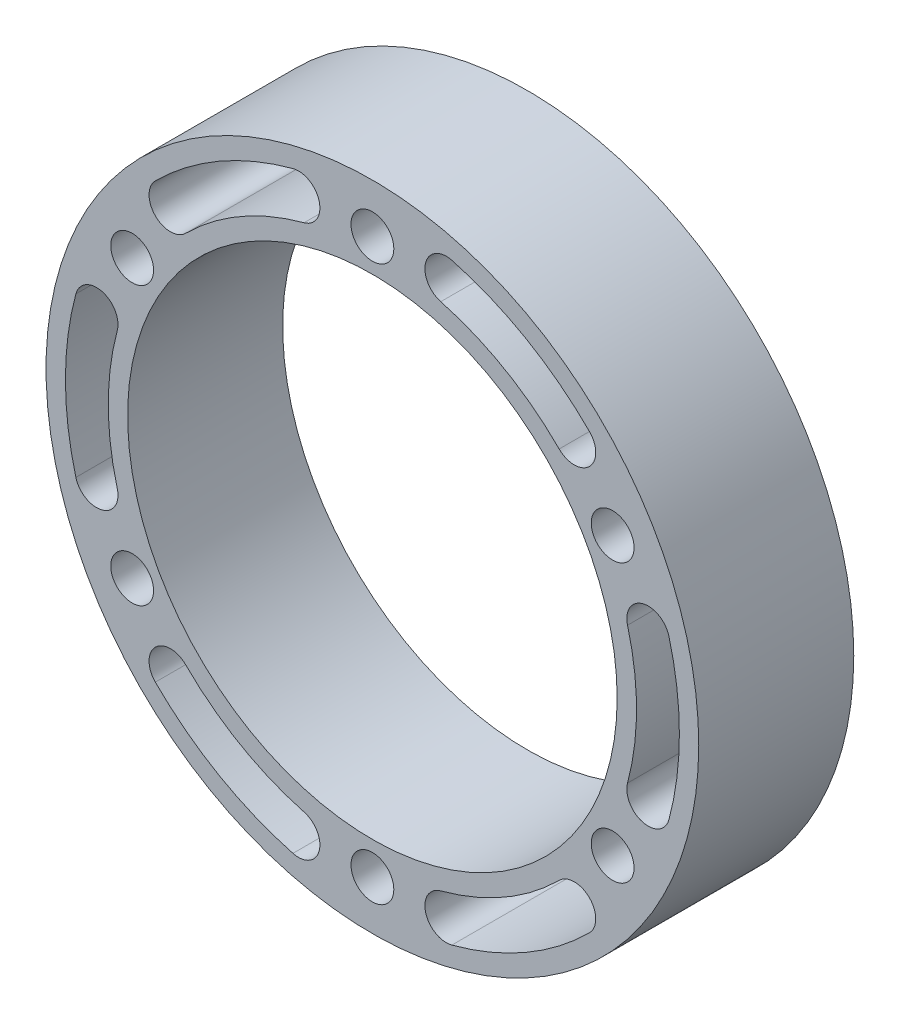
SolidWorks part; units mm, degrees
material "6061-T6 (SS)"
ref_plane "Front Plane" through (0, 0, 0) normal (0, 0, 1) x (1, 0, 0)
ref_plane "Top Plane" through (0, 0, 0) normal (0, 1, 0) x (1, 0, 0)
ref_plane "Right Plane" through (0, 0, 0) normal (1, 0, 0) x (0, 0, -1)
sketch "Sketch1" plane through (0, 0, 0) normal (0, 0, 1) x (1, 0, 0)
  line L0 (0, 0) -> (0, 34) construction
  line L1 (0, 0) -> (-24.7487, 24.7487) construction
  line L2 (0, 0) -> (-9.0587, 33.8074) construction
  line L3 (-29.4449, 17) -> (0, 0) construction
  line L4 (0, 0) -> (-33.8074, -9.0587) construction
  line L5 (-29.4449, -17) -> (0, 0) construction
  circle A0 centre (0, 0) radius 30
  circle A1 centre (0, 0) radius 40
  circle A2 centre (0, 0) radius 34 construction
  circle A3 centre (0, 34) radius 2.625
  circle A4 centre (29.4449, 17) radius 2.625
  circle A5 centre (29.4449, -17) radius 2.625
  circle A6 centre (0, -34) radius 2.625
  circle A7 centre (-29.4449, -17) radius 2.625
  circle A8 centre (-29.4449, 17) radius 2.625
  arc A15 (-9.0587, 33.8074) -> (-24.7487, 24.7487) centre (0, 0) ccw construction
  arc A16 (-9.7381, 36.343) -> (-26.6049, 26.6049) centre (0, 0) ccw
  arc A17 (-8.3793, 31.2718) -> (-22.8926, 22.8926) centre (0, 0) ccw
  arc A18 (-8.3793, 31.2718) -> (-9.7381, 36.343) centre (-9.0587, 33.8074) ccw
  arc A19 (-26.6049, 26.6049) -> (-22.8926, 22.8926) centre (-24.7487, 24.7487) ccw
  arc A20 (24.7487, 24.7487) -> (9.0587, 33.8074) centre (0, 0) ccw construction
  arc A21 (26.6049, 26.6049) -> (9.7381, 36.343) centre (0, 0) ccw
  arc A22 (22.8926, 22.8926) -> (8.3793, 31.2718) centre (0, 0) ccw
  arc A23 (22.8926, 22.8926) -> (26.6049, 26.6049) centre (24.7487, 24.7487) ccw
  arc A24 (9.7381, 36.343) -> (8.3793, 31.2718) centre (9.0587, 33.8074) ccw
  arc A25 (33.8074, -9.0587) -> (33.8074, 9.0587) centre (0, 0) ccw construction
  arc A26 (36.343, -9.7381) -> (36.343, 9.7381) centre (0, 0) ccw
  arc A27 (31.2718, -8.3793) -> (31.2718, 8.3793) centre (0, 0) ccw
  arc A28 (31.2718, -8.3793) -> (36.343, -9.7381) centre (33.8074, -9.0587) ccw
  arc A29 (36.343, 9.7381) -> (31.2718, 8.3793) centre (33.8074, 9.0587) ccw
  arc A30 (9.0587, -33.8074) -> (24.7487, -24.7487) centre (0, 0) ccw construction
  arc A31 (9.7381, -36.343) -> (26.6049, -26.6049) centre (0, 0) ccw
  arc A32 (8.3793, -31.2718) -> (22.8926, -22.8926) centre (0, 0) ccw
  arc A33 (8.3793, -31.2718) -> (9.7381, -36.343) centre (9.0587, -33.8074) ccw
  arc A34 (26.6049, -26.6049) -> (22.8926, -22.8926) centre (24.7487, -24.7487) ccw
  arc A35 (-24.7487, -24.7487) -> (-9.0587, -33.8074) centre (0, 0) ccw construction
  arc A36 (-26.6049, -26.6049) -> (-9.7381, -36.343) centre (0, 0) ccw
  arc A37 (-22.8926, -22.8926) -> (-8.3793, -31.2718) centre (0, 0) ccw
  arc A38 (-22.8926, -22.8926) -> (-26.6049, -26.6049) centre (-24.7487, -24.7487) ccw
  arc A39 (-9.7381, -36.343) -> (-8.3793, -31.2718) centre (-9.0587, -33.8074) ccw
  arc A40 (-33.8074, 9.0587) -> (-33.8074, -9.0587) centre (0, 0) ccw construction
  arc A41 (-36.343, 9.7381) -> (-36.343, -9.7381) centre (0, 0) ccw
  arc A42 (-31.2718, 8.3793) -> (-31.2718, -8.3793) centre (0, 0) ccw
  arc A43 (-31.2718, 8.3793) -> (-36.343, 9.7381) centre (-33.8074, 9.0587) ccw
  arc A44 (-36.343, -9.7381) -> (-31.2718, -8.3793) centre (-33.8074, -9.0587) ccw
  point P9 (-17.5, 30.3109)
  point P31 (17.5, 30.3109)
  point P32 (0, 0)
  point P39 (35, 0)
  point P46 (17.5, -30.3109)
  point P53 (-17.5, -30.3109)
  point P60 (-35, 0)
  point P65 (0, 0)
  dimension "D1" = 60
  dimension "D2" = 80
  dimension "D3" = 68
  dimension "D4" = 5.25
  dimension "D8" = 2.625
  dimension "D6" = 15
  dimension "D7" = 15
  dimension "D9" = 35
  dimension "D5" = 6
  dimension "D10" = 6
extrude "Boss-Extrude1" add sketch "Sketch1" along normal blind 19
